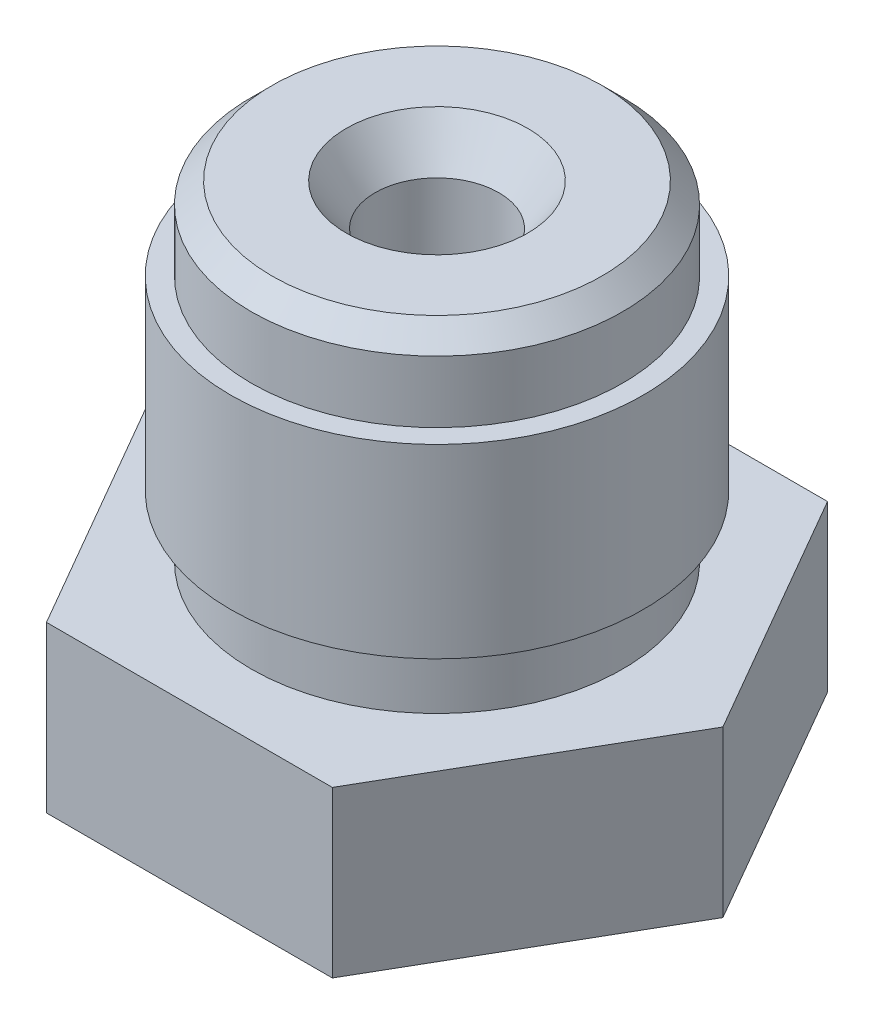
SolidWorks part; units mm, degrees
material "Brass"
ref_plane "Front Plane" through (0, 0, 0) normal (0, 0, 1) x (1, 0, 0)
ref_plane "Top Plane" through (0, 0, 0) normal (0, 1, 0) x (1, 0, 0)
ref_plane "Right Plane" through (0, 0, 0) normal (1, 0, 0) x (0, 0, -1)
sketch "Sketch1" plane through (0, 0, 0) normal (0, 0, 1) x (1, 0, 0)
  line L0 (0, -3.5) -> (0, 3.5) construction
  line L1 (0.2, -3.5) -> (0.2, -2.9)
  line L2 (0.2, -2.9) -> (0.75, -1.9474)
  line L3 (2.25, 3.5) -> (2.25, 2.5)
  line L4 (2.25, 2.5) -> (2.5, 2.5)
  line L5 (0.75, -1.9474) -> (0.75, 3)
  line L6 (0.75, 3) -> (1.1001, 3.5)
  line L7 (1.1001, 3.5) -> (2.25, 3.5)
  line L8 (2.25, 0.25) -> (2.5, 0.25)
  line L9 (2.5, 2.5) -> (2.5, 0.25)
  line L11 (2.25, 0.25) -> (2.25, -0.5)
  line L12 (2.25, -0.5) -> (3, -0.5)
  line L13 (3, -0.5) -> (3, -2.5)
  line L14 (3, -2.5) -> (1.1002, -2.5)
  line L15 (1.1002, -2.5) -> (0.4, -3.5)
  line L16 (0.4, -3.5) -> (0.2, -3.5)
  dimension "D2" = 125
  dimension "D3" = 1
  dimension "A" = 0.4
  dimension "D4" = 1.5
  dimension "D5" = 6
  dimension "D6" = 3
  dimension "D7" = 125
  dimension "D8" = 0.5
  dimension "D9" = 30
  dimension "C" = 0.6
  dimension "D10" = 2
  dimension "B" = 0.8
  dimension "D11" = 4
  dimension "D12" = 0.75
  dimension "D13" = 5
  dimension "D15" = 4.5
revolve "Revolve1" add sketch "Sketch1" angle 360 about L0
sketch "Sketch2" plane through (0, -2.5, 0) normal (0, -1, 0) x (1, 0, 0)
  line L1 (1.7321, 3) -> (-1.7321, 3)
  line L2 (-1.7321, 3) -> (-3.4641, 0)
  line L3 (-3.4641, 0) -> (-1.7321, -3)
  line L4 (-1.7321, -3) -> (1.7321, -3)
  line L5 (1.7321, -3) -> (3.4641, 0)
  line L6 (3.4641, 0) -> (1.7321, 3)
  circle A0 centre (0, 0) radius 3 construction
  circle A1 centre (0, 0) radius 2.6127
  dimension "D1" = 6
extrude "Boss-Extrude1" add sketch "Sketch2" against normal up to surface (2 mm away) up to face at (0, -0.5, -2.25)
chamfer "Chamfer1" distance 0.25 angle 45 1 edges at (0, 3.5, -2.25)
